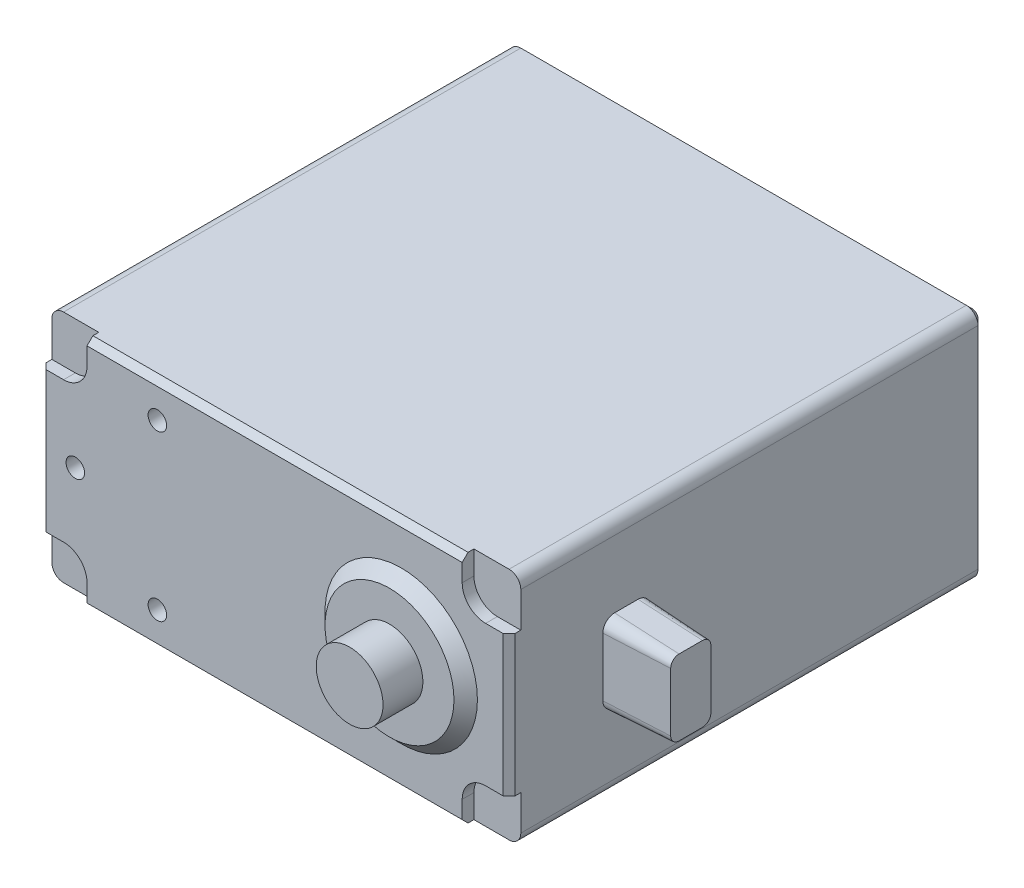
SolidWorks part; units mm, degrees
ref_plane "Plan de face" through (0, 0, 0) normal (0, 0, 1) x (1, 0, 0)
ref_plane "Plan de dessus" through (0, 0, 0) normal (0, 1, 0) x (1, 0, 0)
ref_plane "Plan de droite" through (0, 0, 0) normal (1, 0, 0) x (0, 0, -1)
sketch "Esquisse1" plane through (0, 0, 0) normal (0, 0, 1) x (1, 0, 0)
  line L1 (-15.7182, 10.1847) -> (24.2818, 10.1847)
  line L2 (-15.7182, 10.1847) -> (-15.7182, -9.8153)
  line L3 (-15.7182, -9.8153) -> (24.2818, -9.8153)
  line L4 (24.2818, 10.1847) -> (24.2818, -9.8153)
  dimension "D1" = 40
  dimension "D2" = 20
extrude "Boss.-Extru.1" add sketch "Esquisse1" against normal blind 40.5
sketch "Esquisse2" plane through (0, 0, 0) normal (0, 0, 1) x (1, 0, 0)
  line L0 (-15.7182, 10.1847) -> (-15.7182, -9.8153) construction
  line L1 (24.2818, 10.1847) -> (-15.7182, 10.1847) construction
  circle A0 centre (-12.7182, 0.1847) radius 0.79
  circle A1 centre (-5.7182, 7.1847) radius 0.79
  circle A2 centre (-5.7182, -6.8153) radius 0.79
  point P6 (0, 0)
  point P7 (0, 0)
  point P8 (0, 0)
  point P13 (0, 0)
  dimension "D1" = 1.58
  dimension "D2" = 7
  dimension "D3" = 14
  dimension "D4" = 7
  dimension "D5" = 3
  dimension "D6" = 10
extrude "Enlèv. mat.-Extru.1" cut sketch "Esquisse2" against normal blind 5
sketch "Esquisse3" plane through (0, 0, -40.5) normal (0, 0, -1) x (-1, 0, 0)
  line L1 (-24.2818, 10.1847) -> (15.7182, 10.1847) construction
  line L2 (15.7182, 10.1847) -> (15.7182, -9.8153) construction
  circle A0 centre (-1.7818, 7.6847) radius 0.79
  circle A1 centre (13.2182, 7.6847) radius 0.79
  circle A2 centre (13.2182, -7.3153) radius 0.79
  circle A3 centre (-1.7818, -7.3153) radius 0.79
  point P8 (0, 0)
  point P9 (0, 0)
  point P10 (-18.546, -4.3433)
  point P11 (-7.4494, -5.2506)
  point P12 (0, 0)
  point P13 (0, 0)
  point P14 (-18.7554, 5.2877)
  point P15 (0, 0)
  point P16 (-13.3118, -2.8777)
  point P17 (-18.1273, 5.5669)
  point P20 (-21.2818, 8.1491)
  dimension "D1" = 1.58
  dimension "D2" = 15
  dimension "D3" = 15
  dimension "D4" = 2.5
  dimension "D5" = 2.5
extrude "Enlèv. mat.-Extru.2" cut sketch "Esquisse3" against normal blind 5
sketch "Esquisse4" plane through (0, 0, 0) normal (0, 0, 1) x (1, 0, 0)
  line L1 (-15.7182, 10.1847) -> (-11.7182, 10.1847)
  line L2 (-15.7182, 10.1847) -> (-15.7182, 6.1847)
  line L3 (-15.7182, 6.1847) -> (-13.7182, 6.1847)
  line L4 (-11.7182, 10.1847) -> (-11.7182, 8.1847)
  line L5 (-15.7182, -9.8153) -> (-11.7182, -9.8153)
  line L6 (-15.7182, -9.8153) -> (-15.7182, -5.8153)
  line L7 (-15.7182, -5.8153) -> (-13.7182, -5.8153)
  line L8 (-11.7182, -9.8153) -> (-11.7182, -7.8153)
  line L9 (24.2818, -9.8153) -> (20.2818, -9.8153)
  line L10 (24.2818, -9.8153) -> (24.2818, -5.8153)
  line L11 (24.2818, -5.8153) -> (22.2818, -5.8153)
  line L12 (20.2818, -9.8153) -> (20.2818, -7.8153)
  line L13 (24.2818, 10.1847) -> (20.2818, 10.1847)
  line L14 (24.2818, 10.1847) -> (24.2818, 6.1847)
  line L15 (24.2818, 6.1847) -> (22.2818, 6.1847)
  line L16 (20.2818, 10.1847) -> (20.2818, 8.1847)
  arc A1 (-13.7182, -5.8153) -> (-11.7182, -7.8153) centre (-13.7182, -7.8153) cw
  arc A2 (20.2818, -7.8153) -> (22.2818, -5.8153) centre (22.2818, -7.8153) cw
  arc A3 (20.2818, 8.1847) -> (22.2818, 6.1847) centre (22.2818, 8.1847) ccw
  arc A4 (-13.7182, 6.1847) -> (-11.7182, 8.1847) centre (-13.7182, 8.1847) ccw
  point P22 (-13.4678, 6.1847)
  point P23 (22.0313, 7.9342)
  dimension "D3" = 2
  dimension "D1" = 4
  dimension "D2" = 4
extrude "Enlèv. mat.-Extru.3" cut sketch "Esquisse4" against normal blind 1
fillet "Congé1" radius 1 4 edges at (-15.7182, -9.8153, -20.75) (24.2818, -9.8153, -20.75) (24.2818, 10.1847, -20.75) (-15.7182, 10.1847, -20.75)
sketch "Esquisse5" plane through (0, 0, 0) normal (0, 0, 1) x (1, 0, 0)
  line L0 (20.2818, 10.1847) -> (-11.7182, 10.1847) construction
  line L1 (24.2818, -5.8153) -> (24.2818, 6.1847) construction
  circle A0 centre (15.0818, 0.1847) radius 6.5
  dimension "D1" = 13
  dimension "D2" = 10
  dimension "D3" = 9.2
extrude "Boss.-Extru.2" add sketch "Esquisse5" along normal blind 1 draft 45 contours A0
sketch "Esquisse6" plane through (0, 0, 1) normal (0, 0, 1) x (1, 0, 0)
  circle A0 centre (15.0818, 0.1847) radius 2.85
  circle A1 centre (15.0818, 0.1847) radius 5.5 construction
  dimension "D1" = 5.7
extrude "Boss.-Extru.3" add sketch "Esquisse6" along normal blind 3.4 and the other way blind 45.4
sketch "Esquisse7" plane through (0, 0, -40.5) normal (0, 0, -1) x (-1, 0, 0)
  circle A3 centre (-15.0818, 0.1847) radius 6.5 construction
  circle A4 centre (-15.0818, 0.1847) radius 6.5
extrude "Boss.-Extru.4" add sketch "Esquisse7" along normal blind 1 draft 45
chamfer "Chanfrein1" distance 0.5 angle 45 12 edges at (4.2818, 10.1847, 0) (-15.7182, 0.1847, 0) (4.2818, -9.8153, 0) (24.2818, 0.1847, 0) (-15.4253, 9.8918, -40.5) (-15.7182, 0.1847, -40.5) (-15.4253, -9.5224, -40.5) (4.2818, -9.8153, -40.5) (23.9889, -9.5224, -40.5) (24.2818, 0.1847, -40.5) (23.9889, 9.8918, -40.5) (4.2818, 10.1847, -40.5)
sketch "Esquisse8" plane through (24.2818, 0, 0) normal (1, 0, 0) x (0, 0, -1)
  line L0 (0, -5.8153) -> (0, 6.1847) construction
  line L1 (9, 3.4636) -> (11, 3.4636)
  line L2 (8, 2.4636) -> (8, -2.5364)
  line L3 (9, -3.5364) -> (11, -3.5364)
  line L4 (12, 2.4636) -> (12, -2.5364)
  arc A0 (8, -2.5364) -> (9, -3.5364) centre (9, -2.5364) ccw
  arc A1 (11, -3.5364) -> (12, -2.5364) centre (11, -2.5364) ccw
  arc A2 (12, 2.4636) -> (11, 3.4636) centre (11, 2.4636) ccw
  arc A3 (8, 2.4636) -> (9, 3.4636) centre (9, 2.4636) cw
  dimension "D2" = 1
  dimension "D1" = 8
  dimension "D3" = 4
extrude "Boss.-Extru.5" add sketch "Esquisse8" along normal blind 5.5 draft 3
